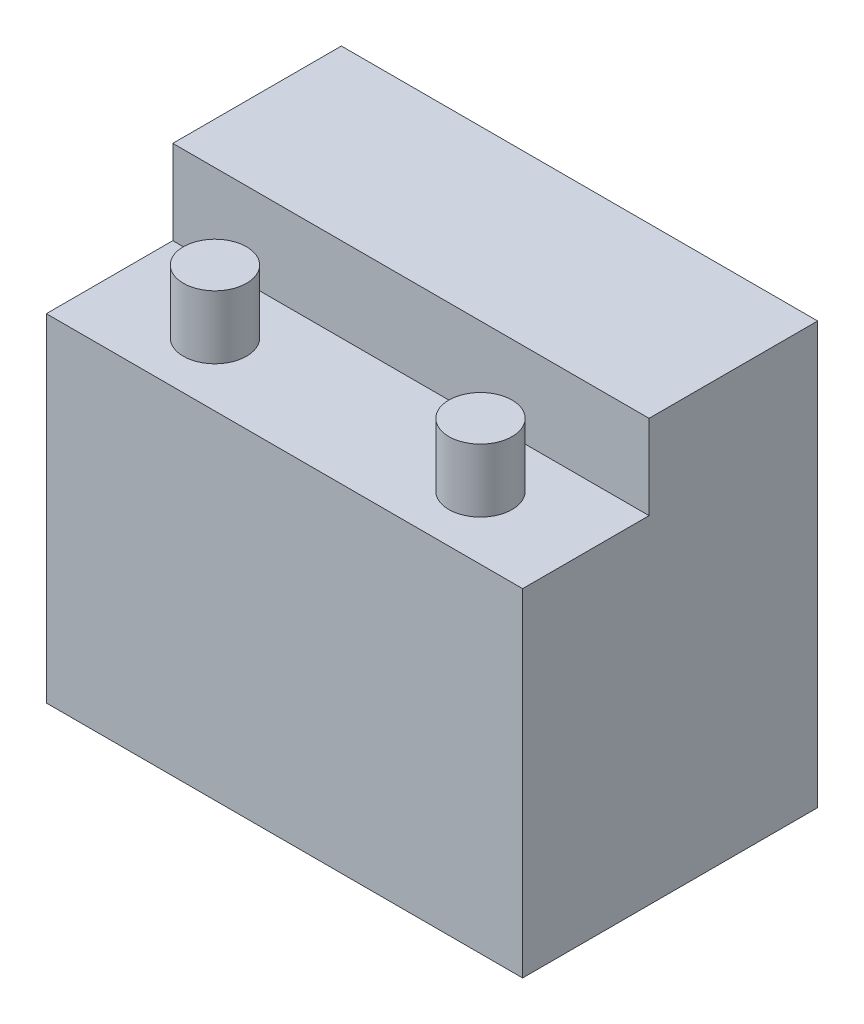
SolidWorks part; units mm, degrees
ref_plane "Front Plane" through (0, 0, 0) normal (0, 0, 1) x (1, 0, 0)
ref_plane "Top Plane" through (0, 0, 0) normal (0, 1, 0) x (1, 0, 0)
ref_plane "Right Plane" through (0, 0, 0) normal (1, 0, 0) x (0, 0, -1)
sketch "Sketch1" plane through (0, 0, 0) normal (0, 1, 0) x (1, 0, 0)
  line L1 (-56.5, -35) -> (56.5, -35)
  line L2 (-56.5, -35) -> (-56.5, 35)
  line L3 (-56.5, 35) -> (56.5, 35)
  line L4 (56.5, -35) -> (56.5, 35)
  line L5 (-56.5, -35) -> (56.5, 35) construction
  line L6 (-56.5, 35) -> (56.5, -35) construction
  point P0 (0, 0)
  dimension "D1" = 113
  dimension "D2" = 70
extrude "Boss-Extrude1" add sketch "Sketch1" along normal blind 100
sketch "Sketch2" plane through (0, 100, 0) normal (0, 1, 0) x (1, 0, 0)
  line L0 (-56.5, 35) -> (-56.5, -35) construction
  line L1 (56.5, -35) -> (-56.5, -35)
  line L2 (56.5, -35) -> (56.5, -5)
  line L3 (56.5, -5) -> (-56.5, -5)
  line L4 (-56.5, -35) -> (-56.5, -5)
  dimension "D1" = 30
extrude "Cut-Extrude2" cut sketch "Sketch2" against normal blind 20
sketch "Sketch3" plane through (0, 80, 0) normal (0, 1, 0) x (1, 0, 0)
  line L0 (-56.5, -20) -> (56.5, -20) construction
  line L1 (-56.5, -5) -> (-56.5, -35) construction
  line L2 (56.5, -35) -> (56.5, -5) construction
  circle A0 centre (-31.5, -20) radius 7.5
  circle A1 centre (31.5, -20) radius 7.5
  dimension "D1" = 15
  dimension "D2" = 25
  dimension "D3" = 25
extrude "Boss-Extrude2" add sketch "Sketch3" along normal blind 15
